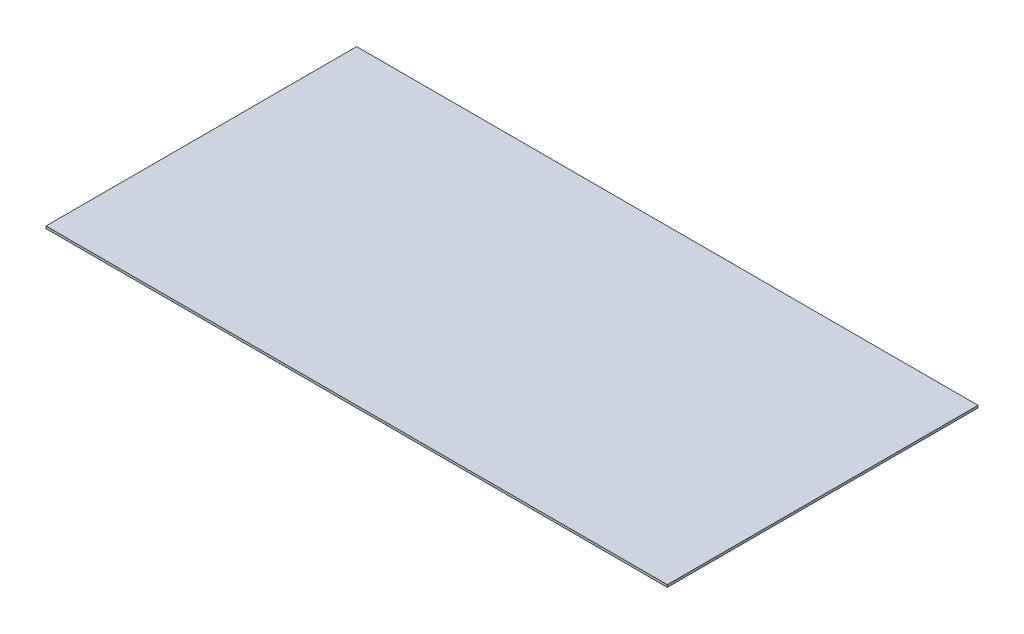
SolidWorks part; units mm, degrees
ref_plane "Front Plane" through (0, 0, 0) normal (0, 0, 1) x (1, 0, 0)
ref_plane "Top Plane" through (0, 0, 0) normal (0, 1, 0) x (1, 0, 0)
ref_plane "Right Plane" through (0, 0, 0) normal (1, 0, 0) x (0, 0, -1)
sketch "Sketch1" plane through (0, 0, 0) normal (0, 1, 0) x (1, 0, 0)
  line L1 (0, 0) -> (800, 0)
  line L2 (0, 0) -> (0, 400)
  line L3 (0, 400) -> (800, 400)
  line L4 (800, 0) -> (800, 400)
  dimension "D1" = 400
  dimension "D2" = 800
extrude "Boss-Extrude1" add sketch "Sketch1" along normal blind 3
